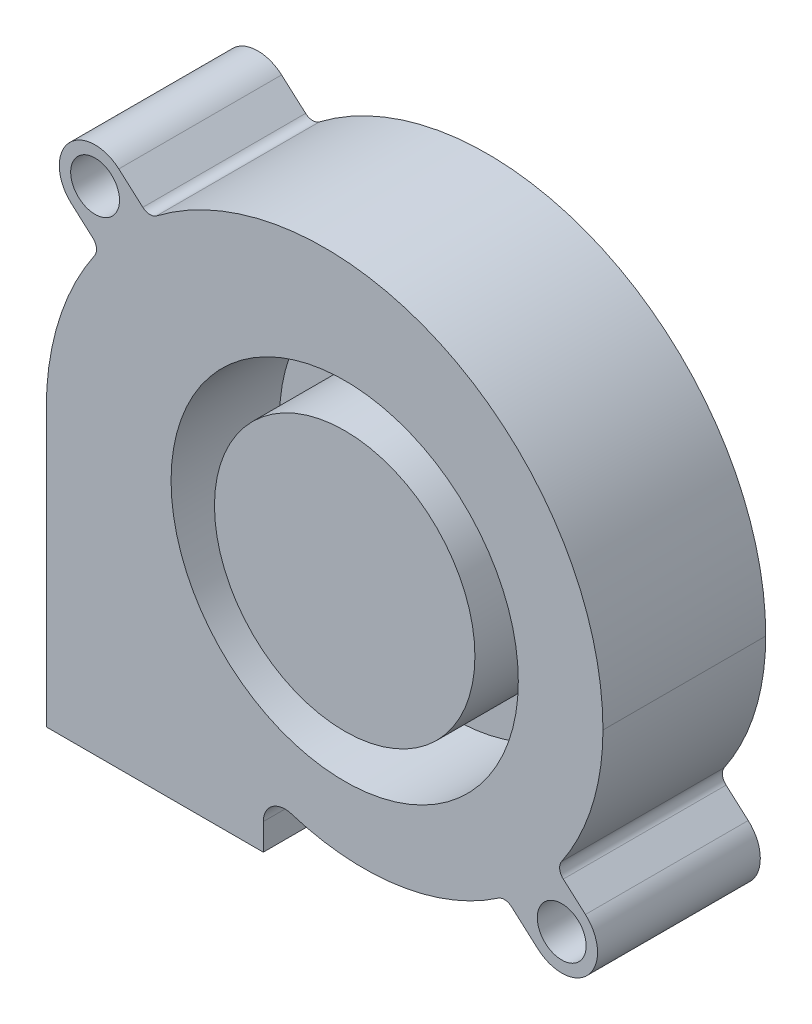
SolidWorks part; units mm, degrees
ref_plane "Płaszczyzna XY" through (0, 0, 0) normal (0, 0, 1) x (1, 0, 0)
ref_plane "Płaszczyzna XZ" through (0, 0, 0) normal (0, 1, 0) x (1, 0, 0)
ref_plane "Płaszczyzna YZ" through (0, 0, 0) normal (1, 0, 0) x (0, 0, -1)
sketch "Szkic1" plane through (0, 0, 0) normal (0, 0, 1) x (1, 0, 0)
  line L0 (-7.5, -25.4) -> (-27.5, -25.4)
  line L1 (-27.5, -25.4) -> (-27.5, 0)
  line L2 (-25.1969, 17.5376) -> (-23.2033, 15.7589)
  line L3 (-20.8147, 22.4728) -> (-18.5989, 20.5146)
  line L4 (-7.5, -22.9558) -> (-7.5, -25.4)
  line L5 (15.377, -18.3185) -> (17.8147, -20.4728)
  line L6 (20.1437, -13.7231) -> (22.1853, -15.5272)
  arc A1 (-18.5989, 20.5146) -> (-17.3331, 20.4667) centre (-17.9367, 21.2639) ccw
  arc A2 (-4.899, -21.0483) -> (14.152, -18.2412) centre (1.7319, 0) ccw
  arc A3 (-20.8147, 22.4728) -> (-25.1969, 17.5376) centre (-23, 20) ccw
  arc A4 (-23.2033, 15.7589) -> (-23.0428, 14.4494) centre (-23.8691, 15.0128) cw
  arc A5 (-27.5, 0) -> (-23.0428, 14.4494) centre (-1.85, 0) cw
  arc A6 (-4.899, -21.0483) -> (-7.5, -22.9558) centre (-5.5, -22.9558) ccw
  arc A7 (14.152, -18.2412) -> (15.377, -18.3185) centre (14.7148, -19.0678) cw
  arc A8 (17.8147, -20.4728) -> (22.1853, -15.5272) centre (20, -18) ccw
  arc A9 (20.1437, -13.7231) -> (19.9791, -12.4113) centre (20.8069, -12.9736) cw
  arc A10 (19.9791, -12.4113) -> (23.8, 0) centre (1.6849, 0.0145) ccw
  arc A11 (23.8, 0) -> (-17.3331, 20.4667) centre (-1.85, 0.0168) ccw
  circle A12 centre (-23, 20) radius 2.25
  circle A13 centre (20, -18) radius 2.25
  point P2 (0, 0)
  point P8 (0, 0)
  point P9 (0, 0)
  point P11 (0, 0)
  point P14 (0, 0)
  point P18 (-17.0513, 20.677)
  dimension "D2" = 25.65
  dimension "D4" = 25.65
  dimension "D6" = 22.1151
  dimension "D7" = 25.4
  dimension "D8" = 4.5
  dimension "D9" = 4.5
  dimension "D10" = 3.3
  dimension "D11" = 3.3
  dimension "D17" = 22.0681
  dimension "D18" = 1
  dimension "D19" = 1
  dimension "D20" = 1
  dimension "D21" = 1.0007
  dimension "D25" = 41.1331
  dimension "D30" = 2
  dimension "D1" = 27.5
  dimension "D3" = 23.0428
  dimension "D5" = 1.685
  dimension "D12" = 23
  dimension "D13" = 20
  dimension "D14" = 18
  dimension "D15" = 21.85
  dimension "D16" = 1.7319
  dimension "D22" = 2.7245
  dimension "D23" = 3.2533
  dimension "D24" = 0
  dimension "D26" = 20.4667
  dimension "D27" = 17.3331
  dimension "D28" = 4.899
  dimension "D29" = 2.4442
  dimension "D31" = 20.1437
  dimension "D32" = 15.377
  dimension "D33" = 18.5989
extrude "Dodanie-wyciągnięcie1" add sketch "Szkic1" along normal blind 15
sketch "Szkic2" plane through (0, 0, 15) normal (0, 0, 1) x (1, 0, 0)
  circle A2 centre (0, 0) radius 12
  circle A3 centre (0, 0) radius 16
  dimension "D1" = 32
  dimension "D2" = 24
extrude "Wytnij-wyciągnięcie1" cut sketch "Szkic2" against normal blind 10 contours A3 | A2
